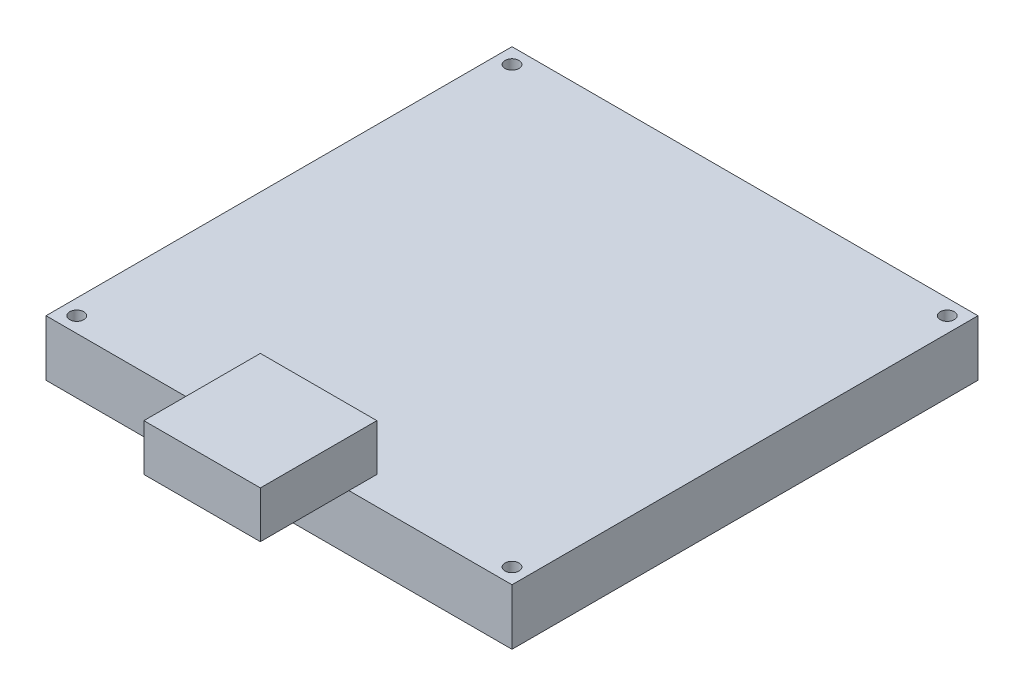
SolidWorks part; units mm, degrees
ref_plane "Front Plane" through (0, 0, 0) normal (0, 0, 1) x (1, 0, 0)
ref_plane "Top Plane" through (0, 0, 0) normal (0, 1, 0) x (1, 0, 0)
ref_plane "Right Plane" through (0, 0, 0) normal (1, 0, 0) x (0, 0, -1)
sketch "Sketch1" plane through (0, 0, 0) normal (0, 1, 0) x (1, 0, 0)
  line L1 (0, 0) -> (100, 0)
  line L2 (0, 0) -> (0, 100)
  line L3 (0, 100) -> (100, 100)
  line L4 (100, 0) -> (100, 100)
  circle A1 centre (96.7, 96.7) radius 1.5
  circle A2 centre (96.7, 3.3) radius 1.5
  circle A3 centre (3.3, 96.7) radius 1.5
  circle A4 centre (3.3, 3.3) radius 1.5
  dimension "D3" = 3
  dimension "D1" = 100
  dimension "D2" = 100
  dimension "D4" = 3.3
  dimension "D5" = 3.3
  dimension "D6" = 3.3
  dimension "D7" = 3.3
extrude "Boss-Extrude1" add sketch "Sketch1" along normal blind 12 contours L1 L4 L3 L2 A4 A3 A2 A1 | A3
sketch "Sketch2" plane through (0, 12, 0) normal (0, 1, 0) x (1, 0, 0)
  line L0 (0, 0) -> (0, 100) construction
  line L1 (65, 6) -> (40, 6)
  line L2 (65, 6) -> (65, -19)
  line L3 (65, -19) -> (40, -19)
  line L4 (40, 6) -> (40, -19)
  line L5 (0, 0) -> (100, 0) construction
  dimension "D1" = 40
  dimension "D2" = 6
  dimension "D3" = 25
  dimension "D4" = 25
extrude "Boss-Extrude2" add sketch "Sketch2" along normal blind 10
